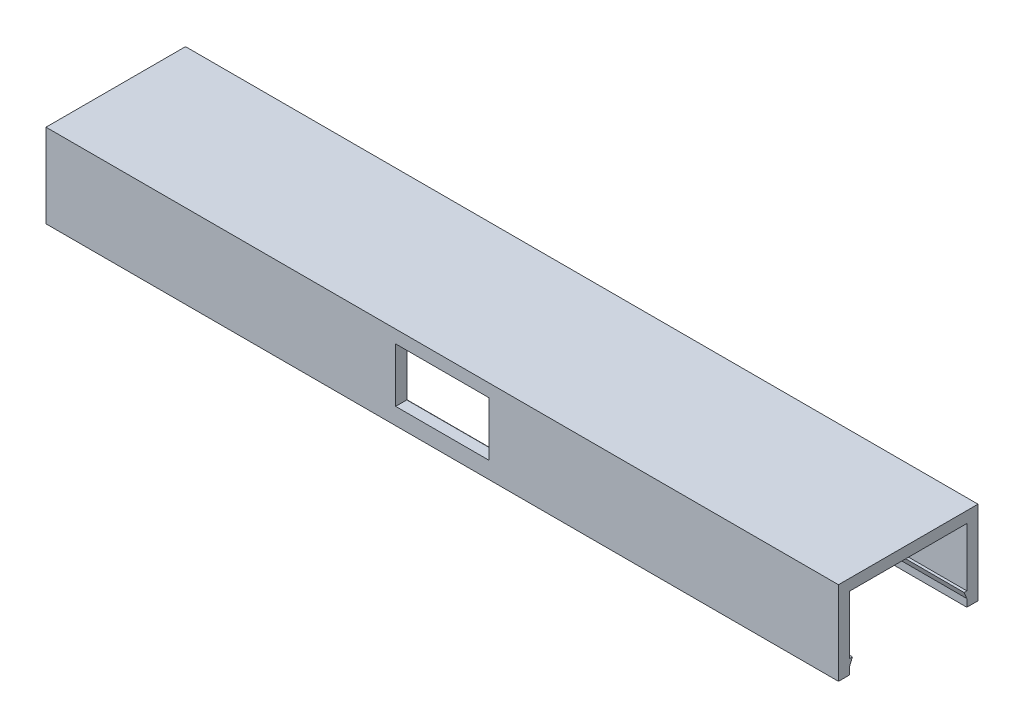
SolidWorks part; units mm, degrees
ref_plane "Front Plane" through (0, 0, 0) normal (0, 0, 1) x (1, 0, 0)
ref_plane "Top Plane" through (0, 0, 0) normal (0, 1, 0) x (1, 0, 0)
ref_plane "Right Plane" through (0, 0, 0) normal (1, 0, 0) x (0, 0, -1)
sketch "Croquis1" plane through (0, 0, 0) normal (0, 1, 0) x (1, 0, 0)
  line L0 (-71, -12.5) -> (-71, 12.5)
  line L1 (-71, -12.5) -> (71, -12.5)
  line L2 (-71, 12.5) -> (71, 12.5)
  line L3 (71, -12.5) -> (71, 12.5)
  line L4 (-71, -12.5) -> (71, 12.5) construction
  line L5 (-71, 12.5) -> (71, -12.5) construction
  line L6 (71, -10.35) -> (71, 10.35)
  line L7 (71, -10.35) -> (-71, -10.35)
  line L8 (71, 10.35) -> (-71, 10.35)
  line L9 (-71, -10.35) -> (-71, 10.35)
  line L10 (71, -10.35) -> (-71, 10.35) construction
  line L11 (71, 10.35) -> (-71, -10.35) construction
  point P1 (0, 0)
  point P2 (0, 0)
  dimension "D1" = 142
  dimension "D2" = 25
  dimension "D3" = 142
  dimension "D4" = 2.15
extrude "Saliente-Extruir1" add sketch "Croquis1" along normal blind 15 contours L3 L8 L0 L7 | L8 L3 L2 L0 | L3 L7 L0 L1
sketch "Croquis2" plane through (-71, 0, 0) normal (-1, 0, 0) x (0, 0, 1)
  line L0 (-10.5, 13) -> (-10.5, 0)
  line L1 (-10.5, 13) -> (10.5, 13)
  line L2 (-10.5, 0) -> (10.5, 0)
  line L3 (10.5, 13) -> (10.5, 0)
  line L4 (-10.5, 13) -> (10.5, 0) construction
  line L5 (-10.5, 0) -> (10.5, 13) construction
  line L6 (-12.5, 15) -> (-12.5, 0) construction
  line L11 (12.5, 15) -> (-12.5, 15) construction
  line L13 (12.5, 0) -> (-12.5, 0) construction
  line L14 (12.5, 15) -> (12.5, 0) construction
  point P1 (0, 6.5)
  dimension "D1" = 2
  dimension "D2" = 2
  dimension "D3" = 2
  dimension "D4" = 6.5
extrude "Cortar-Extruir1" cut sketch "Croquis2" against normal blind 230
sketch "Croquis11" plane through (-71, 0, 0) normal (-1, 0, 0) x (0, 0, 1)
  line L0 (-10.5, 1.35) -> (-10.5, 2.55)
  line L1 (-10.5, 0) -> (-12.5, 0) construction
  line L2 (-10.5, 13) -> (-10.5, 0) construction
  line L3 (-10.5, 2.55) -> (-10, 2.55)
  line L4 (-10, 2.55) -> (-10.5, 1.35)
  line L6 (0, 0) -> (0, 8.3198) construction
  line L11 (10.5, 13) -> (-10.5, 13) construction
  line L13 (10, 2.55) -> (10.5, 1.35)
  line L14 (10.5, 2.55) -> (10, 2.55)
  line L15 (10.5, 1.35) -> (10.5, 2.55)
  dimension "D1" = 10.45
  dimension "D2" = 1.35
  dimension "D3" = 0.5
extrude "Saliente-Extruir4" add sketch "Croquis11" against normal up to surface (142 mm away) up to face at (71, 7, 0)
sketch "Croquis12" plane through (0, 0, 12.5) normal (0, 0, 1) x (1, 0, 0)
  line L0 (-8.35, 3) -> (8.35, 3)
  line L1 (-8.35, 3) -> (-8.35, 12.7)
  line L2 (8.35, 3) -> (8.35, 12.7)
  line L3 (-8.35, 12.7) -> (8.35, 12.7)
  line L4 (-8.35, 3) -> (8.35, 12.7) construction
  line L5 (8.35, 3) -> (-8.35, 12.7) construction
  line L6 (-71, 0) -> (71, 0) construction
  point P1 (0, 7.85)
  point P3 (0, 0)
  point P8 (0, 0)
  dimension "D1" = 16.7
  dimension "D2" = 9.7
  dimension "D3" = 3
extrude "Cortar-Extruir2" cut sketch "Croquis12" against normal blind 10
